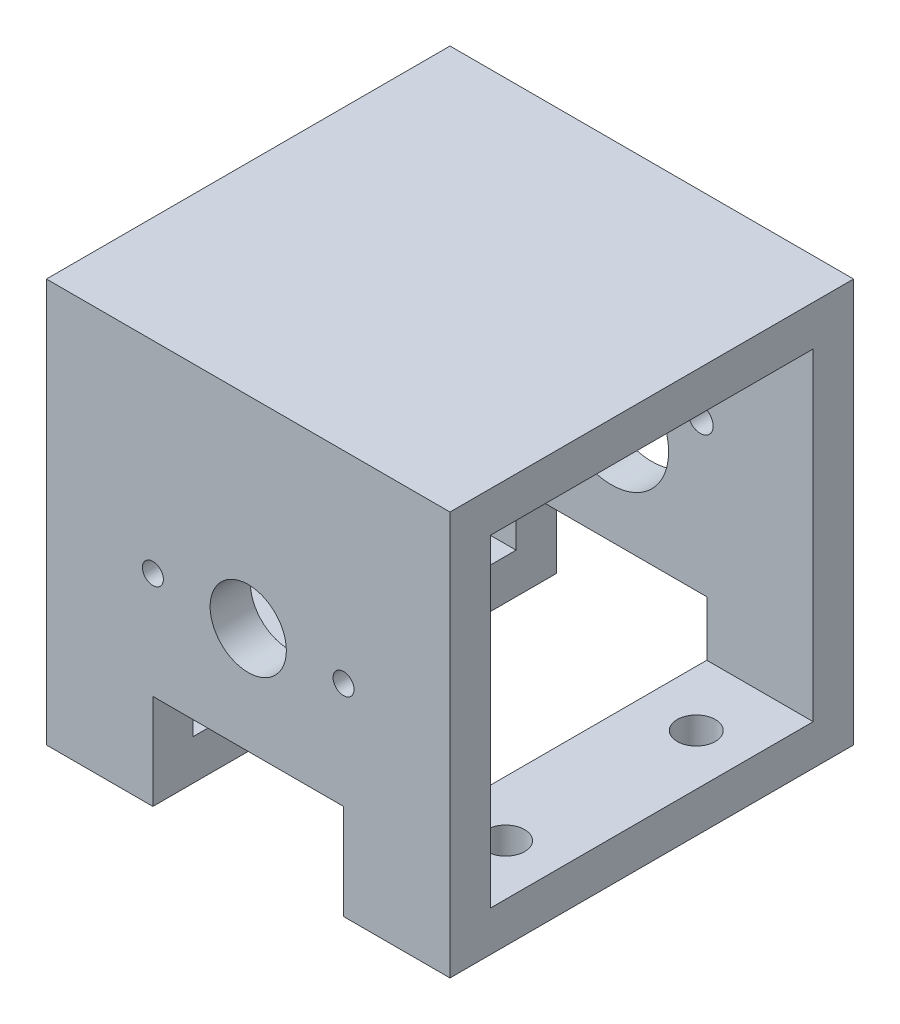
SolidWorks part; units mm, degrees
ref_plane "Front Plane" through (0, 0, 0) normal (0, 0, 1) x (1, 0, 0)
ref_plane "Top Plane" through (0, 0, 0) normal (0, 1, 0) x (1, 0, 0)
ref_plane "Right Plane" through (0, 0, 0) normal (1, 0, 0) x (0, 0, -1)
sketch "Sketch1" plane through (0, 0, 0) normal (0, 1, 0) x (1, 0, 0)
  line L1 (-31.75, -31.75) -> (31.75, -31.75)
  line L2 (-31.75, -31.75) -> (-31.75, 31.75)
  line L3 (-31.75, 31.75) -> (31.75, 31.75)
  line L4 (31.75, -31.75) -> (31.75, 31.75)
  line L5 (-31.75, -31.75) -> (31.75, 31.75) construction
  line L6 (-31.75, 31.75) -> (31.75, -31.75) construction
  point P0 (0, 0)
  dimension "D1" = 63.5
extrude "Boss-Extrude1" add sketch "Sketch1" along normal mid plane 63.5
shell "Shell1" thickness 6.35
sketch "Sketch2" plane through (0, 0, 0) normal (0, 0, 1) x (1, 0, 0)
  line L0 (0, 0) -> (0, -31.75) construction
  line L1 (-31.75, -31.75) -> (31.75, -31.75) construction
  line L3 (-15, -16.75) -> (15, -16.75)
  line L4 (-15, -16.75) -> (-15, -31.75)
  line L5 (-15, -31.75) -> (15, -31.75)
  line L6 (15, -16.75) -> (15, -31.75)
  line L7 (-15, -16.75) -> (15, -31.75) construction
  line L8 (-15, -31.75) -> (15, -16.75) construction
  point P5 (0, -24.25)
  point P10 (11.6992, -23.3458)
  dimension "D1" = 30
  dimension "D2" = 15
extrude "Cut-Extrude1" cut sketch "Sketch2" against normal through all both and the other way through all
sketch "Sketch3" plane through (0, 0, 0) normal (0, 0, 1) x (1, 0, 0)
  circle A0 centre (0, 0) radius 6
  point P3 (0, 0)
  point P6 (0, 0)
  dimension "D1" = 12
extrude "Cut-Extrude2" cut sketch "Sketch3" along normal through all
sketch "Sketch6" plane through (0, 0, 31.75) normal (0, 0, 1) x (1, 0, 0)
  line L0 (-15, 0) -> (15, 0) construction
  point P5 (0, 0)
  dimension "D1" = 30
hole_wizard "M4x0.7 Tapped Hole3" positions "3DSketch3" profile "Sketch7" tap size "M4x0.7" standard "ANSI Metric" end condition up to next
sketch3d "3DSketch3"
  point P0 (-15, 0, 31.75)
  point P3 (15, 0, 31.75)
sketch "Sketch7" plane through (-15, 0, 31.75) normal (1, 0, 0) x (0, -1, 0)
  line L0 (0, 0) -> (0, 6.35)
  line L1 (0, 6.35) -> (1.65, 6.35)
  line L2 (1.65, 6.35) -> (1.65, 0)
  line L5 (1.65, 0) -> (0, 0)
  line L11 (0, -6.35) -> (0, 107.95) construction
  dimension "Thru Tap Drill Dia." = 3.3
  dimension "Thru Tap Drill Depth" = 6.35
cosmetic thread "Hole Thread9" parameters "D2"=4
cosmetic thread "Hole Thread10" parameters "D2"=4
sketch "Sketch8" plane through (0, 0, 0) normal (0, 0, 1) x (1, 0, 0)
  line L0 (-14, 9) -> (14, 9) construction
  line L1 (0, 0) -> (0, 9) construction
  circle A0 centre (0, 0) radius 9
  circle A1 centre (-14, 7) radius 2
  circle A2 centre (14, 7) radius 2
  point P6 (0, 9)
  point P8 (-13.5616, 9)
  point P10 (-13.9827, 7)
  dimension "D1" = 18
  dimension "D2" = 4
  dimension "D3" = 14
extrude "Cut-Extrude3" cut sketch "Sketch8" against normal through all
sketch "Sketch9" plane through (0, 0, 0) normal (0, 1, 0) x (1, 0, 0)
  line L0 (-31.75, 0) -> (31.75, 0) construction
  line L1 (31.75, -31.75) -> (31.75, 31.75) construction
  line L2 (0, -31.75) -> (0, 31.75) construction
  line L3 (15, 31.75) -> (-15, 31.75) construction
  line L4 (-31.75, 31.75) -> (-31.75, -31.75) construction
  circle A0 centre (-23.75, -15) radius 3
  circle A1 centre (23.75, -15) radius 3
  circle A2 centre (23.75, 15) radius 3
  circle A3 centre (-23.75, 15) radius 3
  point P8 (0, 0)
  point P14 (0, 0)
  dimension "D1" = 15
  dimension "D2" = 8
  dimension "D3" = 6
extrude "Cut-Extrude4" cut sketch "Sketch9" against normal through all
